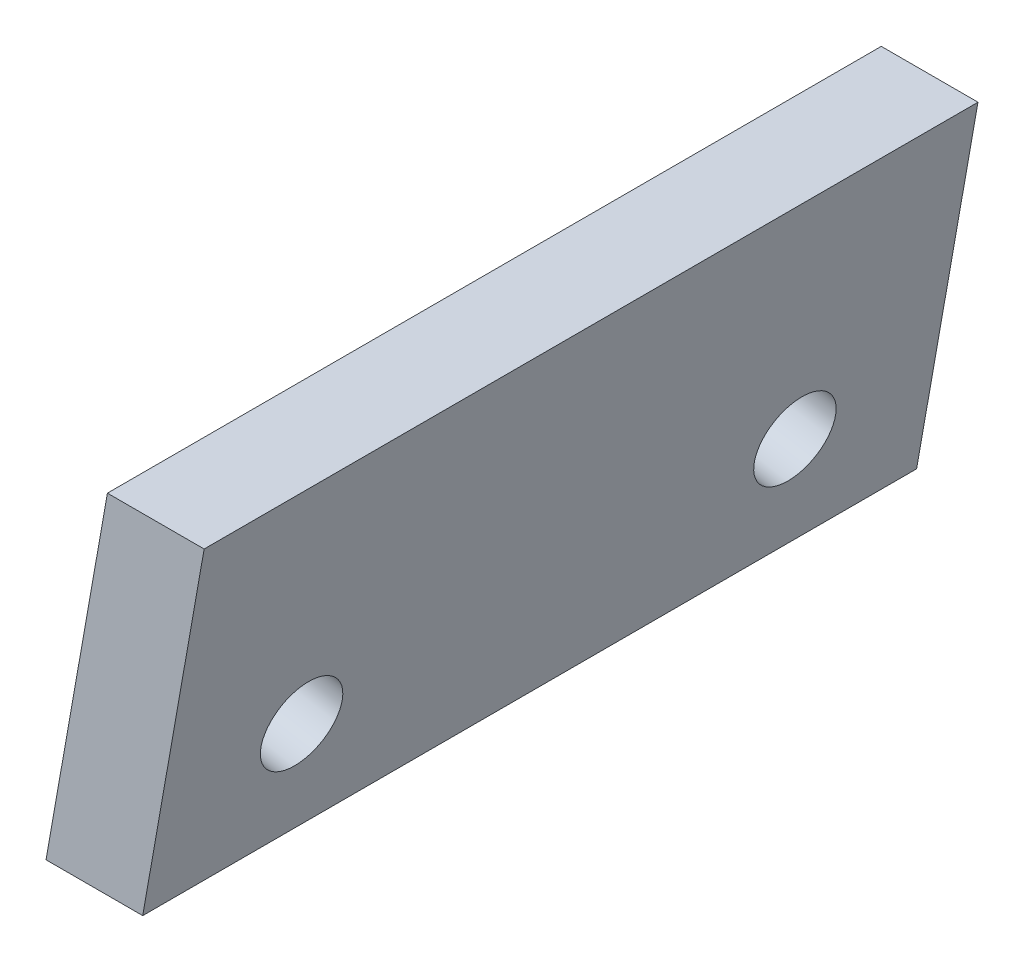
SolidWorks part; units mm, degrees
ref_plane "Front Plane" through (0, 0, 0) normal (0, 0, 1) x (1, 0, 0)
ref_plane "Top Plane" through (0, 0, 0) normal (0, 1, 0) x (1, 0, 0)
ref_plane "Right Plane" through (0, 0, 0) normal (1, 0, 0) x (0, 0, -1)
sketch "Sketch2" plane through (0, 0, 0) normal (0, 0, 1) x (1, 0, 0)
  line L0 (0, 0) -> (2.5, 0)
  line L1 (0, 0) -> (1.5869, 9)
  line L2 (2.5, 0) -> (4.0869, 9)
  line L3 (4.0869, 9) -> (1.5869, 9)
  line L4 (2.5, 0) -> (5.6109, 0) construction
  dimension "D1" = 9
  dimension "D2" = 2.5
  dimension "D3" = 80
extrude "Boss-Extrude2" add sketch "Sketch2" along normal blind 20
sketch "Sketch4" plane through (0, 0, 0) normal (-0.9848, 0.1736, 0) x (0, 0, 1)
  line L1 (20, 9.1388) -> (20, 0) construction
  line L2 (20, 0) -> (0, 0) construction
  circle A0 centre (3.625, 3.2) radius 1.05
  circle A1 centre (16.375, 3.2) radius 1.05
  dimension "D1" = 12.75
  dimension "D2" = 3.625
  dimension "D3" = 3.2
  dimension "D4" = 3.2
  dimension "D5" = 2.1
  dimension "D6" = 2.1
extrude "Cut-Extrude1" cut sketch "Sketch4" against normal through all
